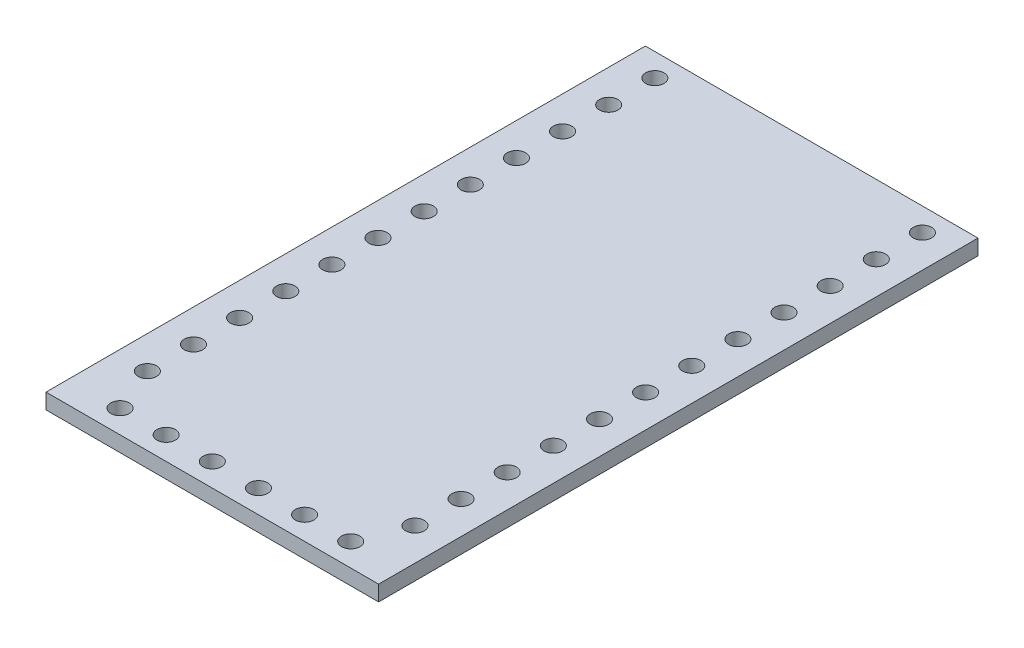
SolidWorks part; units mm, degrees
ref_plane "Front Plane" through (0, 0, 0) normal (0, 0, 1) x (1, 0, 0)
ref_plane "Top Plane" through (0, 0, 0) normal (0, 1, 0) x (1, 0, 0)
ref_plane "Right Plane" through (0, 0, 0) normal (1, 0, 0) x (0, 0, -1)
sketch "Sketch1" plane through (0, 0, 0) normal (0, 1, 0) x (1, 0, 0)
  line L0 (0, 0) -> (0, 78.1833) construction
  line L1 (0, 0) -> (88.2217, 0) construction
  line L2 (-9.1567, 16.5) -> (9.1567, 16.5)
  line L3 (9.1567, 16.5) -> (9.1567, -16.5)
  line L4 (-9.1567, 16.5) -> (-9.1567, -16.5)
  line L5 (-9.1567, -16.5) -> (9.1567, -16.5)
  line L6 (-7.366, 16.5) -> (-7.366, -16.5) construction
  line L7 (-9.1567, -15.23) -> (9.1567, -15.23) construction
  circle A0 centre (-6.35, -15.23) radius 0.508
  circle A1 centre (-3.81, -15.23) radius 0.508
  circle A2 centre (-1.27, -15.23) radius 0.508
  circle A3 centre (1.27, -15.23) radius 0.508
  circle A4 centre (3.81, -15.23) radius 0.508
  circle A5 centre (6.35, -15.23) radius 0.508
  circle A6 centre (-7.366, 15.23) radius 0.508
  circle A7 centre (-7.366, 12.69) radius 0.508
  circle A8 centre (-7.366, 10.15) radius 0.508
  circle A9 centre (-7.366, 7.61) radius 0.508
  circle A10 centre (-7.366, 5.07) radius 0.508
  circle A11 centre (-7.366, 2.53) radius 0.508
  circle A12 centre (-7.366, -0.01) radius 0.508
  circle A13 centre (-7.366, -2.55) radius 0.508
  circle A14 centre (-7.366, -5.09) radius 0.508
  circle A15 centre (-7.366, -7.63) radius 0.508
  circle A16 centre (-7.366, -10.17) radius 0.508
  circle A17 centre (-7.366, -12.71) radius 0.508
  circle A18 centre (7.366, -12.71) radius 0.508
  circle A19 centre (7.366, -10.17) radius 0.508
  circle A20 centre (7.366, -7.63) radius 0.508
  circle A21 centre (7.366, -5.09) radius 0.508
  circle A22 centre (7.366, -2.55) radius 0.508
  circle A23 centre (7.366, -0.01) radius 0.508
  circle A24 centre (7.366, 2.53) radius 0.508
  circle A25 centre (7.366, 5.07) radius 0.508
  circle A26 centre (7.366, 7.61) radius 0.508
  circle A27 centre (7.366, 10.15) radius 0.508
  circle A28 centre (7.366, 12.69) radius 0.508
  circle A29 centre (7.366, 15.23) radius 0.508
  point P8 (0, 16.5)
  point P9 (0, -16.5)
  point P11 (-9.1567, 0)
  point P12 (9.1567, 0)
  dimension "D6" = 1.016
  dimension "D25" = 1.016
  dimension "D1" = 18.3134
  dimension "D2" = 33
  dimension "D3" = 14.732
  dimension "D5" = 1.27
  dimension "D7" = 2.54
  dimension "D8" = 2.54
  dimension "D9" = 2.54
  dimension "D10" = 2.54
  dimension "D11" = 2.54
  dimension "D12" = 1.27
  dimension "D13" = 1.27
  dimension "D14" = 2.54
  dimension "D15" = 2.54
  dimension "D16" = 2.54
  dimension "D17" = 2.54
  dimension "D18" = 2.54
  dimension "D19" = 2.54
  dimension "D20" = 2.54
  dimension "D21" = 2.54
  dimension "D22" = 2.54
  dimension "D23" = 2.54
  dimension "D24" = 2.54
extrude "Boss-Extrude1" add sketch "Sketch1" along normal mid plane 0.85
